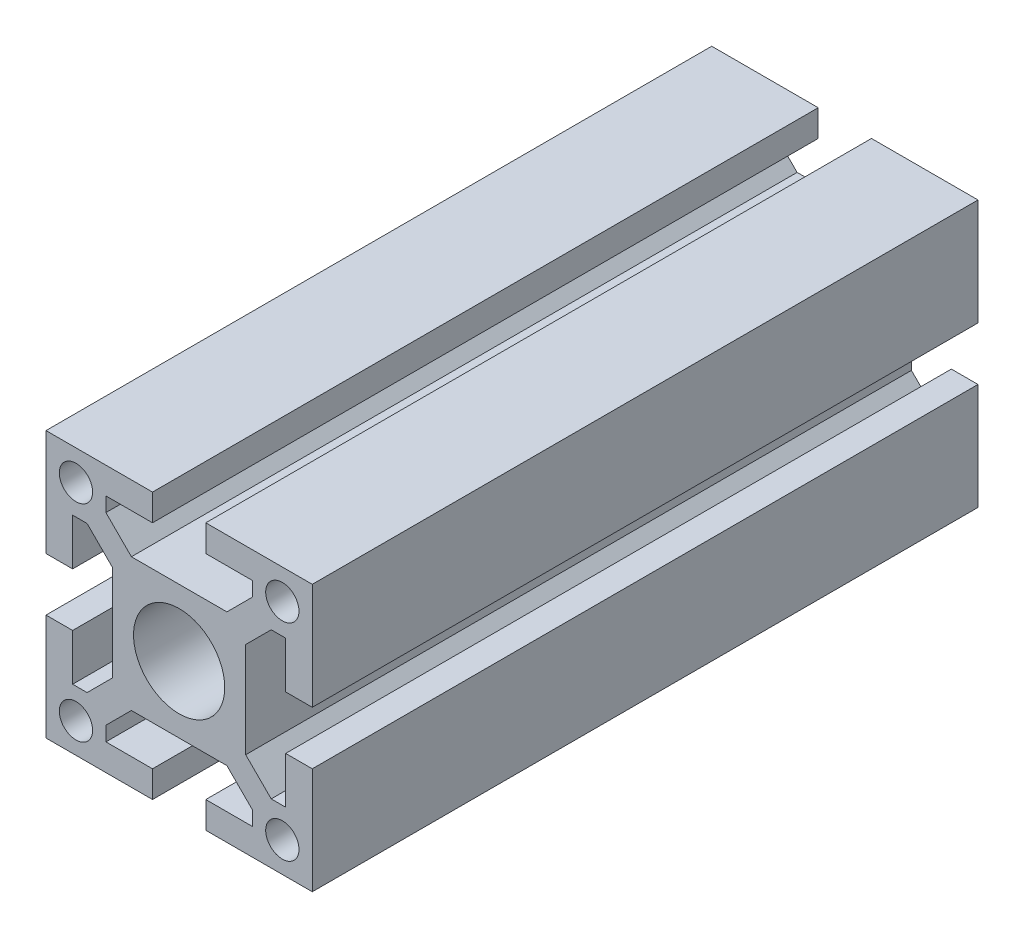
SolidWorks part; units mm, degrees
ref_plane "Front Plane" through (0, 0, 0) normal (0, 0, 1) x (1, 0, 0)
ref_plane "Top Plane" through (0, 0, 0) normal (0, 1, 0) x (1, 0, 0)
ref_plane "Right Plane" through (0, 0, 0) normal (1, 0, 0) x (0, 0, -1)
sketch "Sketch1" plane through (0, 0, 0) normal (0, 0, 1) x (1, 0, 0)
  line L44 (-20, -4) -> (-16, -4)
  line L45 (-16, -4) -> (-16, -11)
  line L46 (-16, -11) -> (-13.8284, -11)
  line L47 (-13.8284, -11) -> (-10, -7.1716)
  line L48 (-10, -7.1716) -> (-10, 7.1716)
  line L49 (-10, 7.1716) -> (-13.8284, 11)
  line L50 (-13.8284, 11) -> (-16, 11)
  line L51 (-16, 11) -> (-16, 4)
  line L52 (-16, 4) -> (-20, 4)
  line L53 (-20, 4) -> (-20, 20)
  line L54 (-20, 20) -> (-4, 20)
  line L55 (-4, 20) -> (-4, 16)
  line L56 (-4, 16) -> (-11, 16)
  line L57 (-11, 16) -> (-11, 13.8284)
  line L58 (-11, 13.8284) -> (-7.1716, 10)
  line L59 (-7.1716, 10) -> (7.1716, 10)
  line L60 (7.1716, 10) -> (11, 13.8284)
  line L61 (11, 13.8284) -> (11, 16)
  line L62 (11, 16) -> (4, 16)
  line L63 (4, 16) -> (4, 20)
  line L64 (4, 20) -> (20, 20)
  line L65 (20, 20) -> (20, 4)
  line L66 (20, 4) -> (16, 4)
  line L67 (16, 4) -> (16, 11)
  line L68 (16, 11) -> (13.8284, 11)
  line L69 (13.8284, 11) -> (10, 7.1716)
  line L70 (10, 7.1716) -> (10, -7.1716)
  line L71 (10, -7.1716) -> (13.8284, -11)
  line L72 (13.8284, -11) -> (16, -11)
  line L73 (16, -11) -> (16, -4)
  line L74 (16, -4) -> (20, -4)
  line L75 (20, -4) -> (20, -20)
  line L76 (20, -20) -> (4, -20)
  line L77 (4, -20) -> (4, -16)
  line L78 (4, -16) -> (11, -16)
  line L79 (11, -16) -> (11, -13.8284)
  line L80 (11, -13.8284) -> (7.1716, -10)
  line L81 (7.1716, -10) -> (-7.1716, -10)
  line L82 (-7.1716, -10) -> (-11, -13.8284)
  line L83 (-11, -13.8284) -> (-11, -16)
  line L84 (-11, -16) -> (-4, -16)
  line L85 (-4, -16) -> (-4, -20)
  line L86 (-4, -20) -> (-20, -20)
  line L87 (-20, -20) -> (-20, -4)
  circle A5 centre (-15.5, -15.5) radius 2.5
  circle A6 centre (-15.5, 15.5) radius 2.5
  circle A7 centre (15.5, -15.5) radius 2.5
  circle A8 centre (15.5, 15.5) radius 2.5
  circle A9 centre (0, 0) radius 6.85
extrude "Extrude1" add sketch "Sketch1" against normal blind 100
